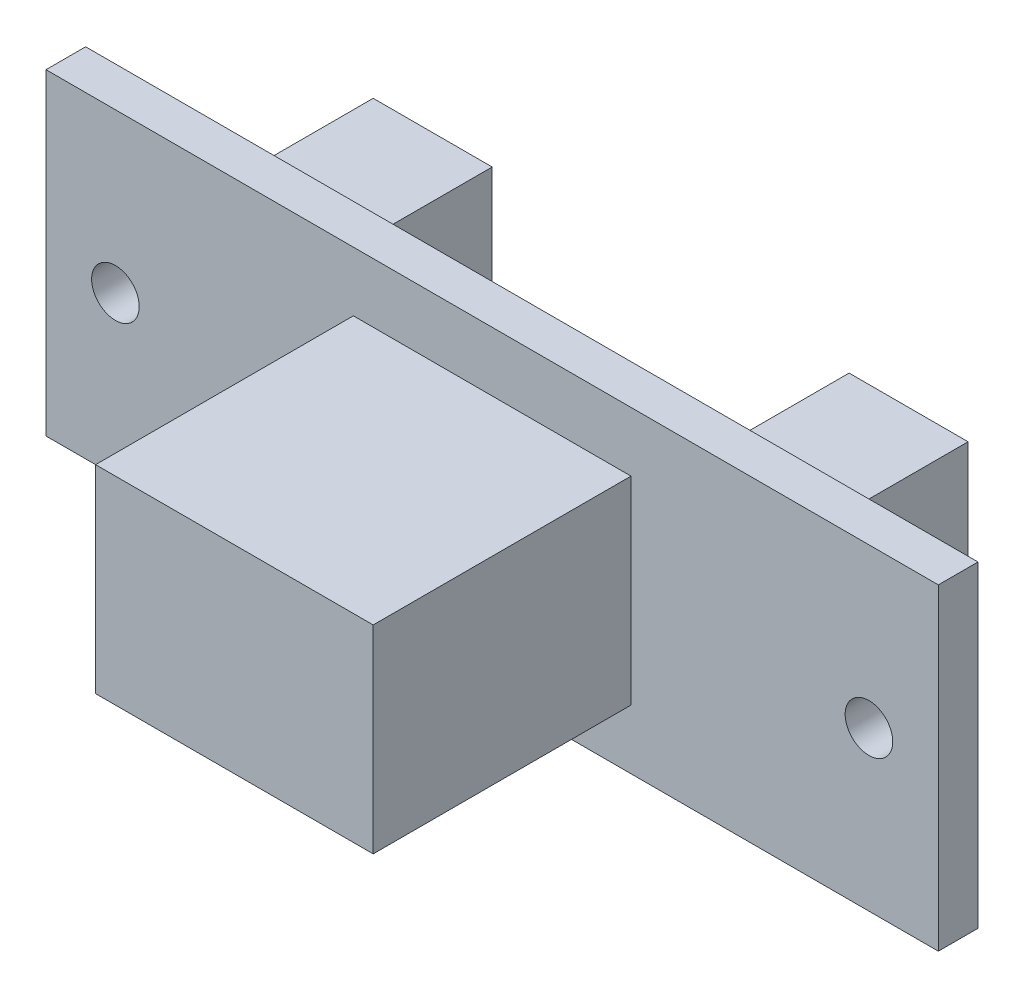
SolidWorks part; units mm, degrees
ref_plane "正面" through (0, 0, 0) normal (0, 0, 1) x (1, 0, 0)
ref_plane "平面" through (0, 0, 0) normal (0, 1, 0) x (1, 0, 0)
ref_plane "右側面" through (0, 0, 0) normal (1, 0, 0) x (0, 0, -1)
sketch "ｽｹｯﾁ1" plane through (0, 0, 0) normal (0, 0, 1) x (1, 0, 0)
  line L1 (22.5, 8) -> (-22.5, 8)
  line L2 (22.5, 8) -> (22.5, -8)
  line L3 (22.5, -8) -> (-22.5, -8)
  line L4 (-22.5, 8) -> (-22.5, -8)
  line L5 (22.5, 8) -> (-22.5, -8) construction
  line L6 (22.5, -8) -> (-22.5, 8) construction
  point P0 (0, 0)
  dimension "D1" = 16
  dimension "D2" = 45
extrude "ﾎﾞｽ - 押し出し1" add sketch "ｽｹｯﾁ1" along normal blind 2
sketch "ｽｹｯﾁ2" plane through (0, 0, 2) normal (0, 0, 1) x (1, 0, 0)
  line L0 (22.5, 8) -> (-22.5, 8) construction
  line L1 (-22.5, 8) -> (-22.5, -8) construction
  line L2 (0, 0) -> (0, -8) construction
  line L3 (-22.5, -8) -> (22.5, -8) construction
  circle A0 centre (-19, 0) radius 1.2
  circle A1 centre (19, 0) radius 1.2
  dimension "D1" = 2.4
  dimension "D2" = 8
  dimension "D3" = 3.5
extrude "ｶｯﾄ - 押し出し1" cut sketch "ｽｹｯﾁ2" against normal blind 2
sketch "ｽｹｯﾁ3" plane through (0, 0, 2) normal (0, 0, 1) x (1, 0, 0)
  line L0 (22.5, 8) -> (-22.5, 8) construction
  line L1 (-7, 5) -> (7, 5)
  line L2 (-7, 5) -> (-7, -5)
  line L3 (-7, -5) -> (7, -5)
  line L4 (7, 5) -> (7, -5)
  line L5 (-7, 5) -> (7, -5) construction
  line L6 (-7, -5) -> (7, 5) construction
  point P0 (0, 0)
  point P7 (2.4571, 1)
  point P8 (0, 1)
  dimension "D1" = 10
  dimension "D2" = 3
  dimension "D3" = 14
extrude "ﾎﾞｽ - 押し出し2" add sketch "ｽｹｯﾁ3" along normal blind 13
sketch "ｽｹｯﾁ4" plane through (0, 0, 2) normal (0, 0, 1) x (1, 0, 0)
  line L0 (0, 0) -> (0, -8) construction
  line L1 (-9, 6) -> (-15, 6)
  line L2 (-9, 6) -> (-9, -6)
  line L3 (-9, -6) -> (-15, -6)
  line L4 (-15, 6) -> (-15, -6)
  line L5 (-9, 6) -> (-15, -6) construction
  line L6 (-9, -6) -> (-15, 6) construction
  line L7 (-22.5, -8) -> (22.5, -8) construction
  line L8 (9, -6) -> (15, -6)
  line L9 (15, 6) -> (15, -6)
  line L10 (9, 6) -> (15, 6)
  line L11 (9, 6) -> (9, -6)
  circle A0 centre (-19, 0) radius 1.2 construction
  point P0 (-12, 0)
  dimension "D1" = 12
  dimension "D2" = 6
  dimension "D3" = 4
extrude "ﾎﾞｽ - 押し出し3" add sketch "ｽｹｯﾁ4" against normal blind 9
